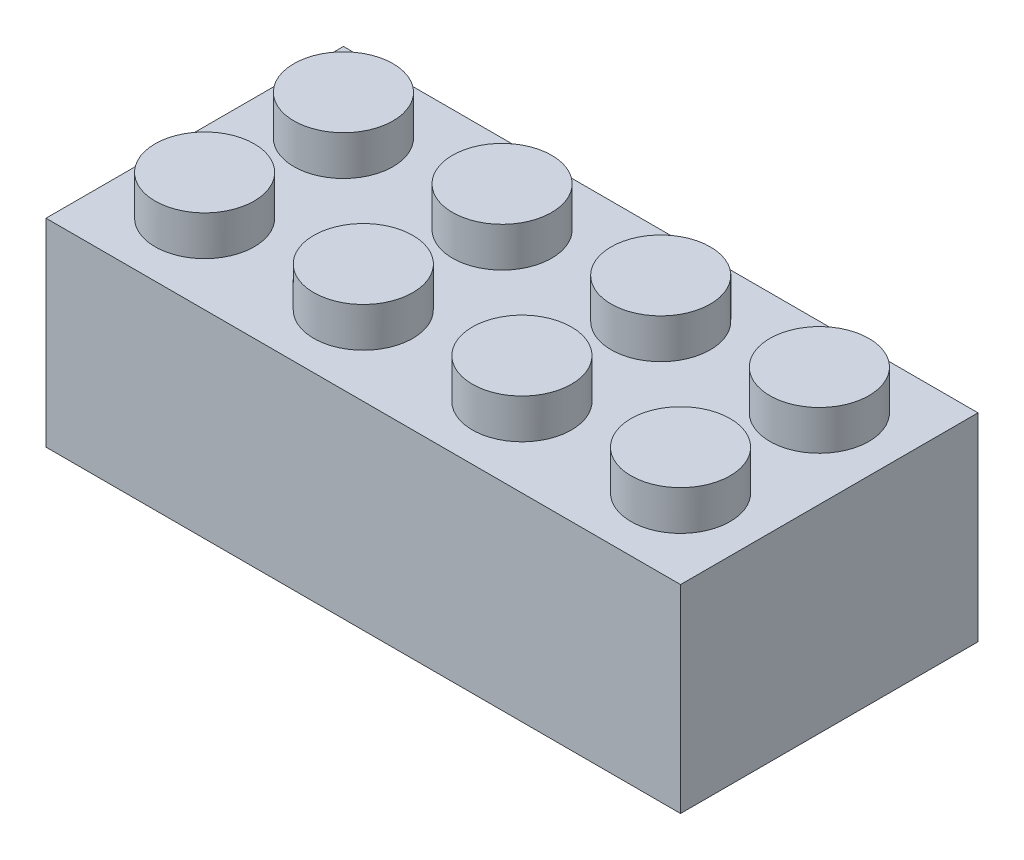
SolidWorks part; units mm, degrees
ref_plane "Front Plane" through (0, 0, 0) normal (0, 0, 1) x (1, 0, 0)
ref_plane "Top Plane" through (0, 0, 0) normal (0, 1, 0) x (1, 0, 0)
ref_plane "Right Plane" through (0, 0, 0) normal (1, 0, 0) x (0, 0, -1)
sketch "Sketch1" plane through (0, 0, 0) normal (0, 1, 0) x (1, 0, 0)
  line L1 (-16, -7.5) -> (16, -7.5)
  line L2 (-16, -7.5) -> (-16, 7.5)
  line L3 (-16, 7.5) -> (16, 7.5)
  line L4 (16, -7.5) -> (16, 7.5)
  line L5 (-16, -7.5) -> (16, 7.5) construction
  line L6 (-16, 7.5) -> (16, -7.5) construction
  point P0 (0, 0)
  dimension "D1" = 32
  dimension "D2" = 15
extrude "Boss-Extrude1" add sketch "Sketch1" along normal blind 10
sketch "Sketch2" plane through (0, 10, 0) normal (0, 1, 0) x (1, 0, 0)
  line L0 (-16, 7.5) -> (-16, -7.5) construction
  line L1 (-16, -7.5) -> (16, -7.5) construction
  line L2 (-5.5, 0) -> (5.5, 0) construction
  circle A0 centre (-12, -3.5) radius 2.5
  circle A1 centre (-4, -3.5) radius 2.5
  circle A2 centre (4, -3.5) radius 2.5
  circle A3 centre (12, -3.5) radius 2.5
  circle A4 centre (12, 3.5) radius 2.5
  circle A5 centre (4, 3.5) radius 2.5
  circle A6 centre (-4, 3.5) radius 2.5
  circle A7 centre (-12, 3.5) radius 2.5
  dimension "D1" = 5
  dimension "D2" = 4
  dimension "D3" = 4
  dimension "D4" = 4
extrude "Boss-Extrude2" add sketch "Sketch2" along normal blind 2
sketch "Sketch3" plane through (0, 0, 0) normal (0, -1, 0) x (1, 0, 0)
  line L0 (-16, 7.5) -> (16, 7.5) construction
  line L1 (-15, -6.5) -> (15, -6.5)
  line L2 (-15, -6.5) -> (-15, 6.5)
  line L3 (-15, 6.5) -> (15, 6.5)
  line L4 (15, -6.5) -> (15, 6.5)
  line L5 (-15, -6.5) -> (15, 6.5) construction
  line L6 (-15, 6.5) -> (15, -6.5) construction
  line L7 (16, 7.5) -> (16, -7.5) construction
  point P0 (0, 0)
  dimension "D1" = 1
  dimension "D2" = 1
extrude "Cut-Extrude1" cut sketch "Sketch3" against normal blind 9
sketch "Sketch4" plane through (0, 9, 0) normal (0, -1, 0) x (1, 0, 0)
  circle A0 centre (0, 0) radius 3.5
  circle A1 centre (0, 0) radius 3
  circle A2 centre (8, 0) radius 3.5
  circle A3 centre (8, 0) radius 3
  circle A4 centre (0, 0) radius 3.5
  circle A5 centre (0, 0) radius 3
  circle A6 centre (-8, 0) radius 3.5
  circle A7 centre (-8, 0) radius 3
  dimension "D1" = 7
  dimension "D2" = 0.5
  dimension "D3" = 2
  dimension "D4" = 2
extrude "Boss-Extrude3" add sketch "Sketch4" along normal up to surface (9 mm away) contours A6 | A7 | A0 | A1 | A2 | A3 up to face at (0, 0, 0)
sketch "Sketch5" plane through (0, 9, 0) normal (0, -1, 0) x (1, 0, 0)
  line L0 (15, 6.5) -> (-15, 6.5) construction
  line L1 (-0.2722, -6.5) -> (0.2722, -6.5)
  line L2 (-0.2722, -6.5) -> (-0.2722, -3.4894)
  line L3 (-0.2722, 6.5) -> (0.2722, 6.5)
  line L4 (0.2722, -6.5) -> (0.2722, -3.4894)
  line L5 (-0.2722, -6.5) -> (0.2722, 6.5) construction
  line L6 (-0.2722, 6.5) -> (0.1097, -2.6188) construction
  line L7 (-0.2722, 3.4894) -> (-0.2722, 6.5)
  line L8 (0.2722, 3.4894) -> (0.2722, 6.5)
  arc A0 (-0.2722, 3.4894) -> (0.2722, 3.4894) centre (0, 0) cw
  circle A1 centre (0, 0) radius 3.5 construction
  arc A2 (-0.2722, -3.4894) -> (0.2722, -3.4894) centre (0, 0) ccw
  point P0 (0, 0)
extrude "Boss-Extrude4" add sketch "Sketch5" along normal blind 7 contours L3 L8 A0 L7 | L1 L4 A2 L2
